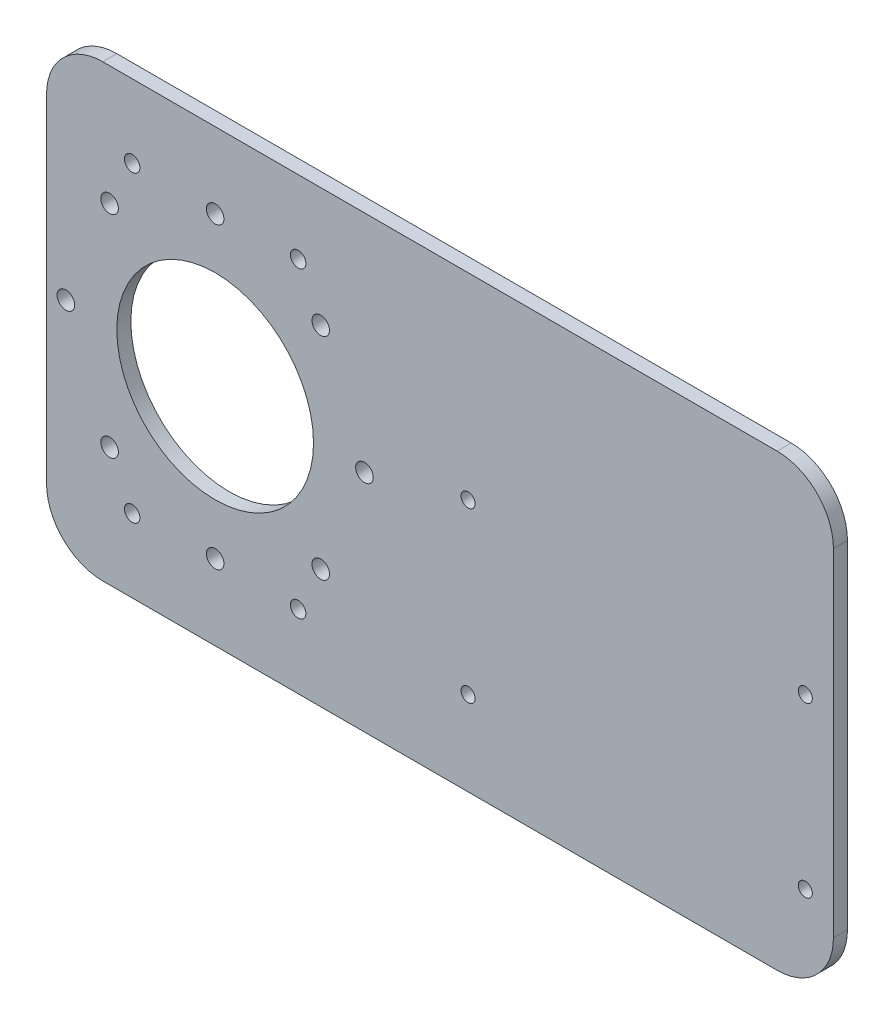
SolidWorks part; units mm, degrees
material "6061 Alloy"
ref_plane "Front Plane" through (0, 0, 0) normal (0, 0, 1) x (1, 0, 0)
ref_plane "Top Plane" through (0, 0, 0) normal (0, 1, 0) x (1, 0, 0)
ref_plane "Right Plane" through (0, 0, 0) normal (1, 0, 0) x (0, 0, -1)
sketch "Sketch1" plane through (0, 0, 0) normal (0, 0, 1) x (1, 0, 0)
  line L1 (0, 0) -> (355.6, 0)
  line L2 (0, 0) -> (0, 203.2)
  line L3 (0, 203.2) -> (355.6, 203.2)
  line L4 (355.6, 0) -> (355.6, 203.2)
  dimension "D1" = 203.2
  dimension "D2" = 355.6
extrude "Boss-Extrude1" add sketch "Sketch1" along normal blind 6.35
sketch "Sketch2" plane through (0, 0, 6.35) normal (0, 0, 1) x (1, 0, 0)
  line L0 (355.6, 203.2) -> (0, 203.2) construction
  line L1 (0, 203.2) -> (0, 0) construction
  circle A0 centre (76.2, 101.6) radius 76.2
  circle A1 centre (76.2, 101.6) radius 44.45
  circle A2 centre (143.6688, 101.6) radius 3.9687
  circle A10 centre (123.9076, 53.8924) radius 3.9687
  circle A11 centre (76.2, 34.1312) radius 3.9687
  circle A12 centre (28.4924, 53.8924) radius 3.9687
  circle A13 centre (8.7312, 101.6) radius 3.9687
  circle A14 centre (28.4924, 149.3076) radius 3.9688
  circle A15 centre (76.2, 169.0687) radius 3.9687
  circle A16 centre (123.9076, 149.3076) radius 3.9688
  dimension "D1" = 152.4
  dimension "D4" = 88.9
  dimension "D5" = 7.9375
  dimension "D6" = 67.4688
  dimension "D2" = 101.6
  dimension "D3" = 76.2
  dimension "D7" = 101.6
  dimension "D8" = 8
extrude "Cut-Extrude1" cut sketch "Sketch2" against normal blind 76.2
sketch "Sketch3" plane through (0, 0, 6.35) normal (0, 0, 1) x (1, 0, 0)
  line L0 (76.2, 170.1) -> (76.2, 33.1) construction
  line L1 (38.6994, 170.1) -> (113.7006, 170.1) construction
  line L2 (38.6994, 170.1) -> (38.6994, 33.1) construction
  line L3 (38.6994, 33.1) -> (113.7006, 33.1) construction
  line L4 (113.7006, 170.1) -> (113.7006, 33.1) construction
  line L5 (113.7006, 101.6) -> (38.6994, 101.6)
  line L6 (0, 203.2) -> (0, 0) construction
  line L7 (355.6, 203.2) -> (0, 203.2) construction
  circle A0 centre (38.6994, 170.1) radius 3.5001
  circle A1 centre (113.7006, 170.1) radius 3.5001
  circle A2 centre (113.7006, 33.1) radius 3.5001
  circle A3 centre (38.6994, 33.1) radius 3.5001
  dimension "D3" = 7.0002
  dimension "D4" = 76.2
  dimension "D1" = 75.0011
  dimension "D2" = 137
  dimension "D5" = 101.6
extrude "Cut-Extrude2" cut sketch "Sketch3" against normal blind 6.35 contours A0 | A1 | A2 | A3
fillet "Fillet1" radius 25.4 4 edges at (0, 203.2, 3.175) (0, 0, 3.175) (355.6, 0, 3.175) (355.6, 203.2, 3.175)
sketch "Sketch5" plane through (0, 0, 0) normal (0, 0, -1) x (-1, 0, 0)
  line L0 (-341.8766, 76.2) -> (-161.8766, 76.2) construction
  line L1 (-25.4, 0) -> (-330.2, 0) construction
  line L2 (-355.6, 25.4) -> (-355.6, 177.8) construction
  circle A0 centre (-342.9, 114.3) radius 3.175
  circle A1 centre (-190.5, 114.3) radius 3.175
  circle A2 centre (-190.5, 38.1) radius 3.175
  circle A3 centre (-342.9, 38.1) radius 3.175
  dimension "D3" = 38.1
  dimension "D1" = 152.4
  dimension "D2" = 76.2
  dimension "D4" = 12.7
extrude "Cut-Extrude4" cut sketch "Sketch5" against normal blind 6.35
